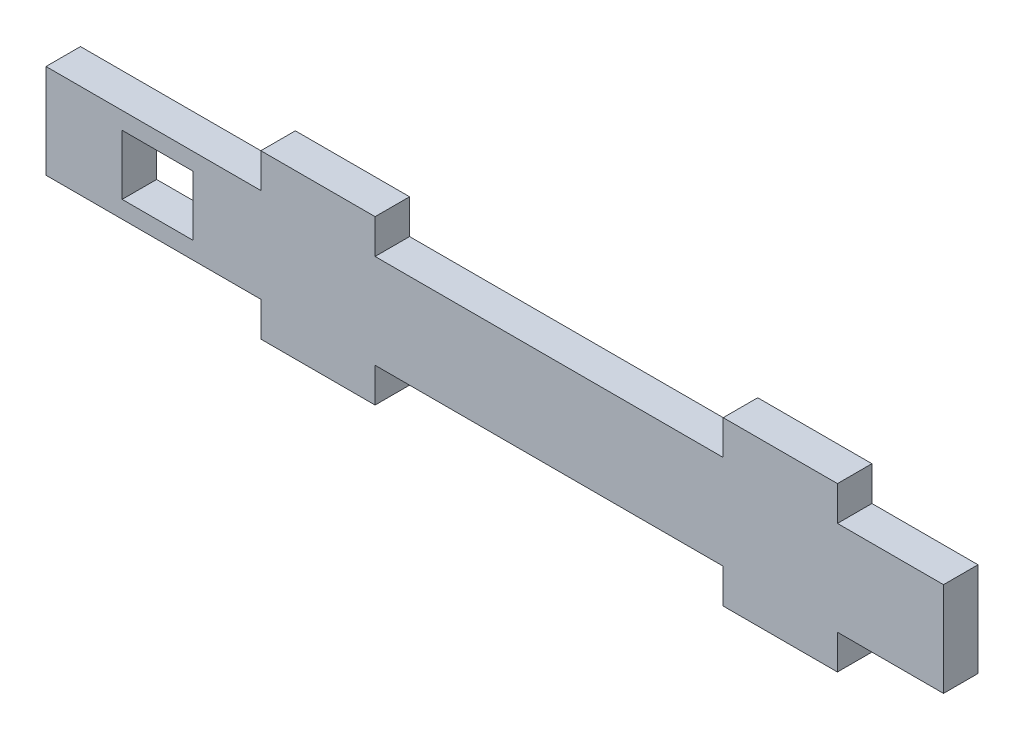
SolidWorks part; units mm, degrees
ref_plane "Front Plane" through (0, 0, 0) normal (0, 0, 1) x (1, 0, 0)
ref_plane "Top Plane" through (0, 0, 0) normal (0, 1, 0) x (1, 0, 0)
ref_plane "Right Plane" through (0, 0, 0) normal (1, 0, 0) x (0, 0, -1)
sketch "Sketch1" plane through (0, 0, 0) normal (0, 0, 1) x (1, 0, 0)
  line L0 (0, 4.33) -> (82.5, 4.33) construction
  line L1 (0, 0) -> (82.5, 0)
  line L2 (0, 0) -> (0, 8.66)
  line L3 (0, 8.66) -> (82.5, 8.66)
  line L4 (82.5, 0) -> (82.5, 8.66)
  line L5 (19.75, 0) -> (30.25, 0)
  line L6 (19.75, 0) -> (19.75, -3.17)
  line L7 (19.75, -3.17) -> (30.25, -3.17)
  line L8 (30.25, 0) -> (30.25, -3.17)
  line L9 (19.75, 8.66) -> (30.25, 8.66)
  line L10 (19.75, 8.66) -> (19.75, 11.83)
  line L11 (19.75, 11.83) -> (30.25, 11.83)
  line L12 (30.25, 8.66) -> (30.25, 11.83)
  line L13 (62.25, 8.66) -> (72.75, 8.66)
  line L14 (62.25, 8.66) -> (62.25, 11.83)
  line L15 (62.25, 11.83) -> (72.75, 11.83)
  line L16 (72.75, 8.66) -> (72.75, 11.83)
  line L17 (62.25, 0) -> (72.75, 0)
  line L18 (62.25, 0) -> (62.25, -3.17)
  line L19 (62.25, -3.17) -> (72.75, -3.17)
  line L20 (72.75, 0) -> (72.75, -3.17)
  line L21 (7, 7.08) -> (13.5, 7.08)
  line L22 (7, 7.08) -> (7, 1.58)
  line L23 (7, 1.58) -> (13.5, 1.58)
  line L24 (13.5, 7.08) -> (13.5, 1.58)
  point P21 (25, 11.83)
  point P28 (7, 4.33)
  point P29 (67.5, 11.83)
  dimension "D1" = 25
  dimension "D2" = 15
  dimension "D3" = 10.5
  dimension "D4" = 15
  dimension "D5" = 3.17
  dimension "D6" = 5.5
  dimension "D7" = 6.5
  dimension "D8" = 7
  dimension "D9" = 82.5
  dimension "D10" = 32
extrude "Boss-Extrude1" add sketch "Sketch1" along normal blind 3.17 contours L0 L2 L1 L4 L24 L23 L22 | L2 L0 L22 L21 L24 L4 L3 | L3 L12 L11 L10 | L8 L1 L6 L7 | L20 L1 L18 L19 | L3 L16 L15 L14
